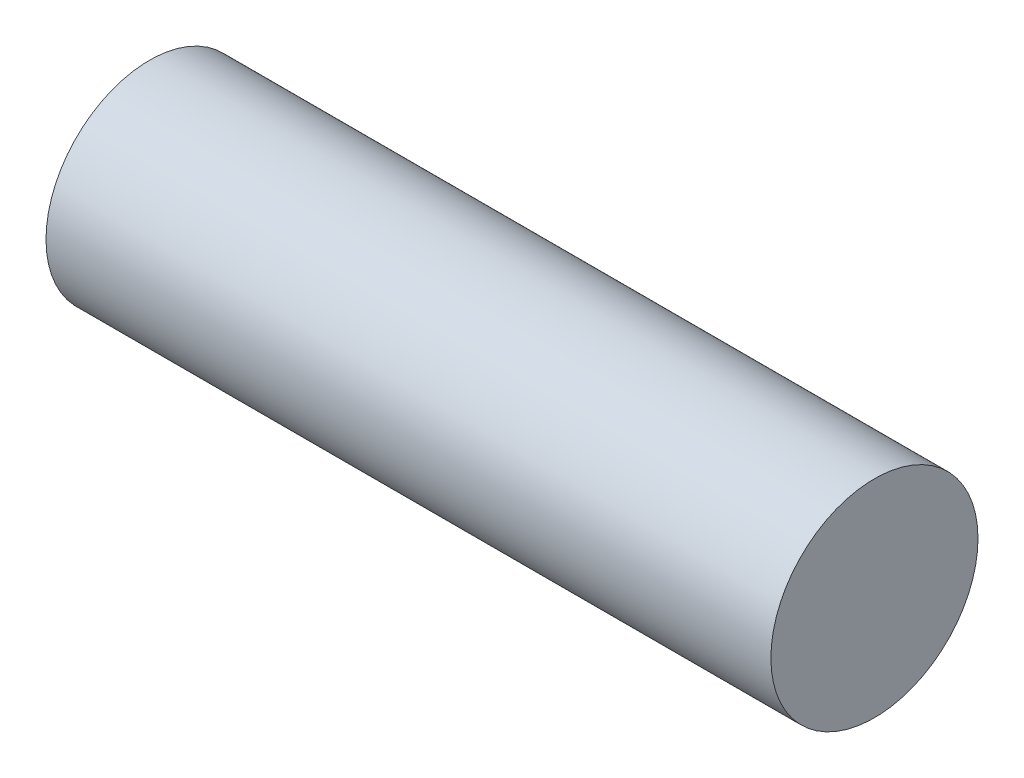
SolidWorks part; units mm, degrees
ref_plane "Front Plane" through (0, 0, 0) normal (0, 0, 1) x (1, 0, 0)
ref_plane "Top Plane" through (0, 0, 0) normal (0, 1, 0) x (1, 0, 0)
ref_plane "Right Plane" through (0, 0, 0) normal (1, 0, 0) x (0, 0, -1)
sketch "Sketch1" plane through (0, 0, 0) normal (1, 0, 0) x (0, 0, -1)
  circle A0 centre (0, 0) radius 10
  dimension "D1" = 20
extrude "Boss-Extrude1" add sketch "Sketch1" along normal blind 70
